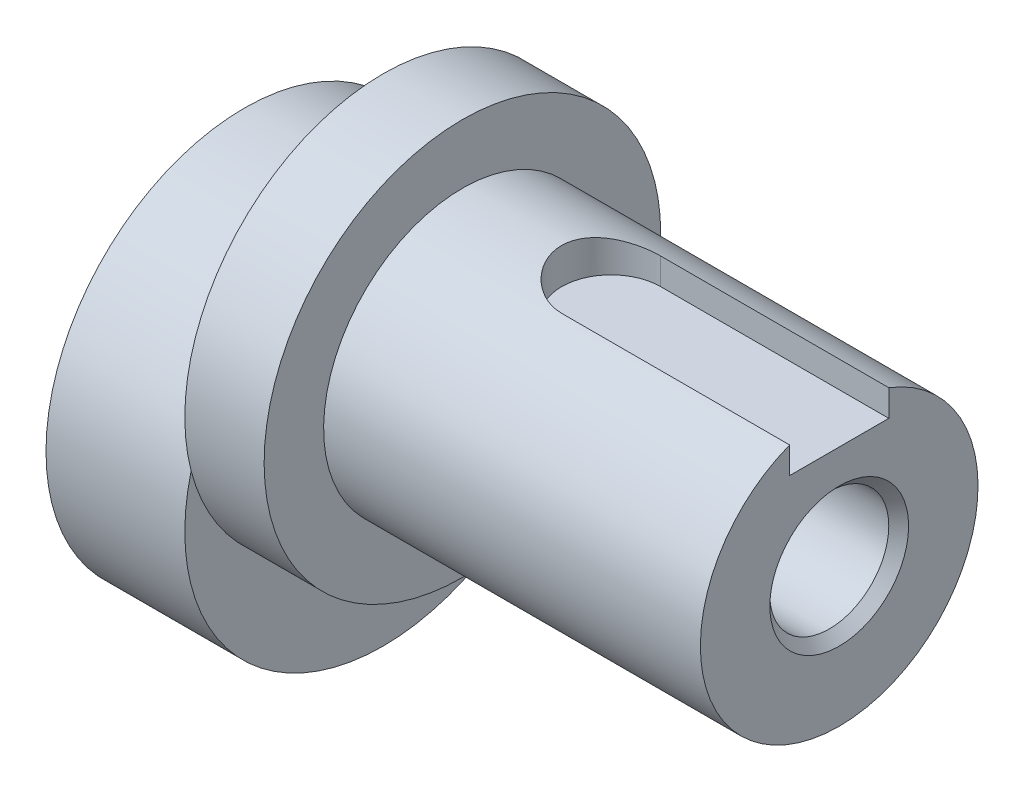
SolidWorks part; units mm, degrees
ref_plane "Front Plane" through (0, 0, 0) normal (0, 0, 1) x (1, 0, 0)
ref_plane "Top Plane" through (0, 0, 0) normal (0, 1, 0) x (1, 0, 0)
ref_plane "Right Plane" through (0, 0, 0) normal (1, 0, 0) x (0, 0, -1)
sketch "Sketch1" plane through (0, 0, 0) normal (1, 0, 0) x (0, 0, -1)
  circle A0 centre (0, 0) radius 10
  dimension "D1" = 20
extrude "Boss-Extrude1" add sketch "Sketch1" along normal blind 7
sketch "Sketch2" plane through (7, 0, 0) normal (1, 0, 0) x (0, 0, -1)
  circle A0 centre (0, 5) radius 10
  point P2 (0, 0)
  dimension "D1" = 20
  dimension "D2" = 5
extrude "Boss-Extrude2" add sketch "Sketch2" along normal blind 4
sketch "Sketch3" plane through (11, 0, 0) normal (1, 0, 0) x (0, 0, -1)
  circle A0 centre (0, 5) radius 7
  dimension "D1" = 14
extrude "Boss-Extrude3" add sketch "Sketch3" along normal blind 19
sketch "Sketch4" plane through (30, 0, 0) normal (1, 0, 0) x (0, 0, -1)
  circle A0 centre (0, 5) radius 3
  dimension "D1" = 6
extrude "Cut-Extrude1" cut sketch "Sketch4" against normal through all
chamfer "Chamfer1" distance 0.5 angle 45 2 edges at (30, 5, -3) (0, 5, -3)
sketch "Sketch5" plane through (0, 0, 0) normal (0, 1, 0) x (1, 0, 0)
  line L0 (30, 0) -> (14.3442, 0) construction
  line L1 (30, -7) -> (30, 7) construction
  line L3 (31, 2.5) -> (18.5, 2.5)
  line L4 (31, 2.5) -> (31, -2.5)
  line L5 (31, -2.5) -> (18.5, -2.5)
  arc A0 (18.5, 2.5) -> (18.5, -2.5) centre (18.5, 0) ccw
  point P10 (16, 0)
  dimension "D1" = 2.5
  dimension "D2" = 14
  dimension "D3" = 1
extrude "Cut-Extrude2" cut sketch "Sketch5" along normal through all from offset 10.2
